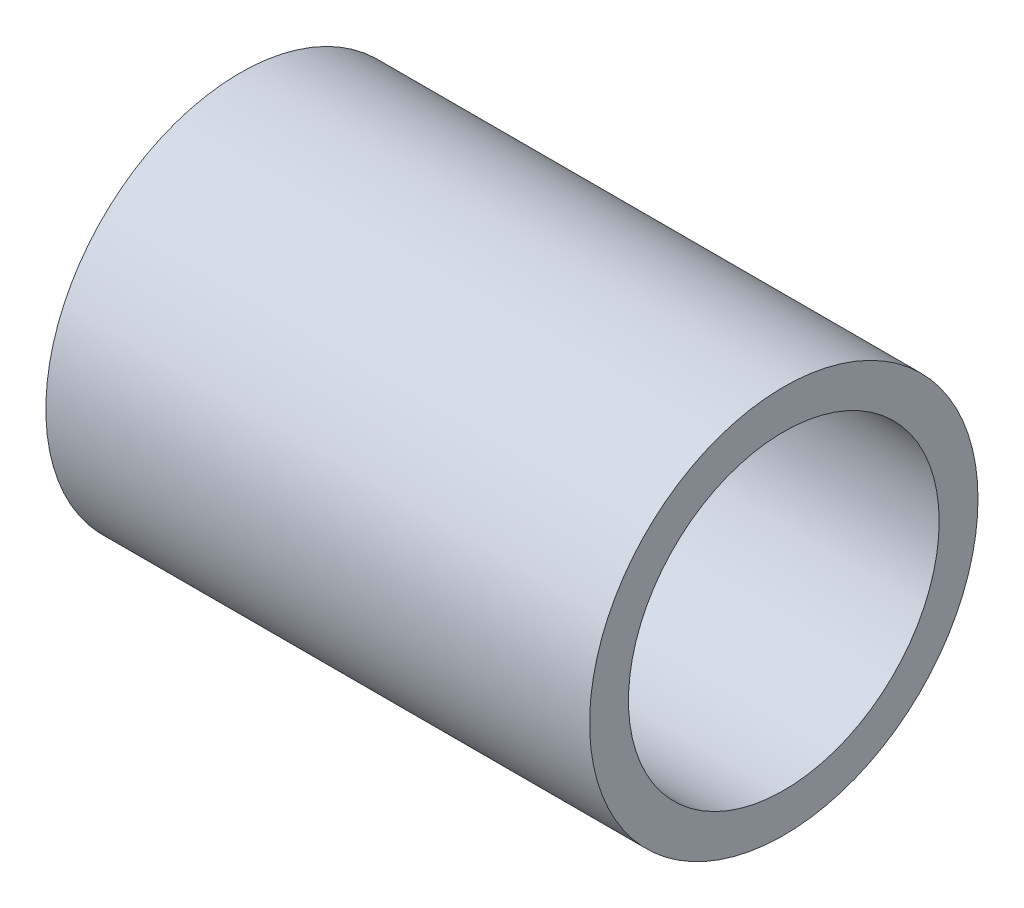
SolidWorks part; units mm, degrees
ref_plane "Front Plane" through (0, 0, 0) normal (0, 0, 1) x (1, 0, 0)
ref_plane "Top Plane" through (0, 0, 0) normal (0, 1, 0) x (1, 0, 0)
ref_plane "Right Plane" through (0, 0, 0) normal (1, 0, 0) x (0, 0, -1)
sketch "Sketch1" plane through (0, 0, 0) normal (1, 0, 0) x (0, 0, -1)
  circle A0 centre (0, 0) radius 2
  circle A1 centre (0, 0) radius 2.5
  dimension "D1" = 4
  dimension "D2" = 5
extrude "Boss-Extrude1" add sketch "Sketch1" along normal blind 7
